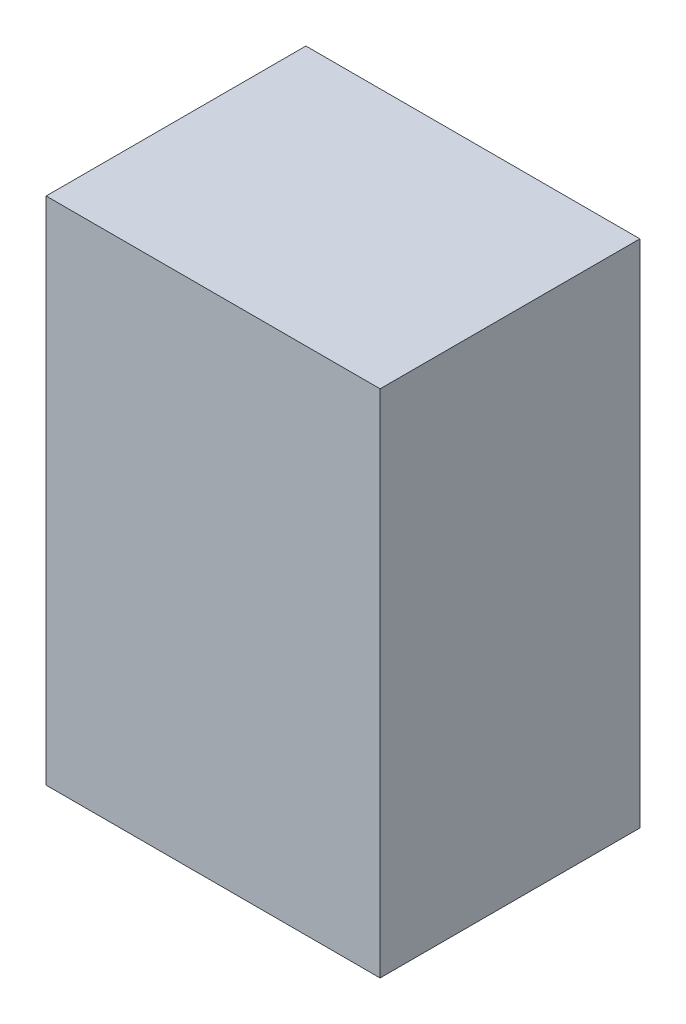
SolidWorks part; units mm, degrees
ref_plane "Front Plane" through (0, 0, 0) normal (0, 0, 1) x (1, 0, 0)
ref_plane "Top Plane" through (0, 0, 0) normal (0, 1, 0) x (1, 0, 0)
ref_plane "Right Plane" through (0, 0, 0) normal (1, 0, 0) x (0, 0, -1)
sketch "Sketch2" plane through (0, 0, 0) normal (0, 1, 0) x (1, 0, 0)
  line L1 (-45.72, -35.56) -> (45.72, -35.56)
  line L2 (-45.72, -35.56) -> (-45.72, 35.56)
  line L3 (-45.72, 35.56) -> (45.72, 35.56)
  line L4 (45.72, -35.56) -> (45.72, 35.56)
  line L5 (-45.72, -35.56) -> (45.72, 35.56) construction
  line L6 (-45.72, 35.56) -> (45.72, -35.56) construction
  point P0 (0, 0)
  dimension "D1" = 91.44
  dimension "D2" = 71.12
extrude "Boss-Extrude1" add sketch "Sketch2" along normal blind 139.7
